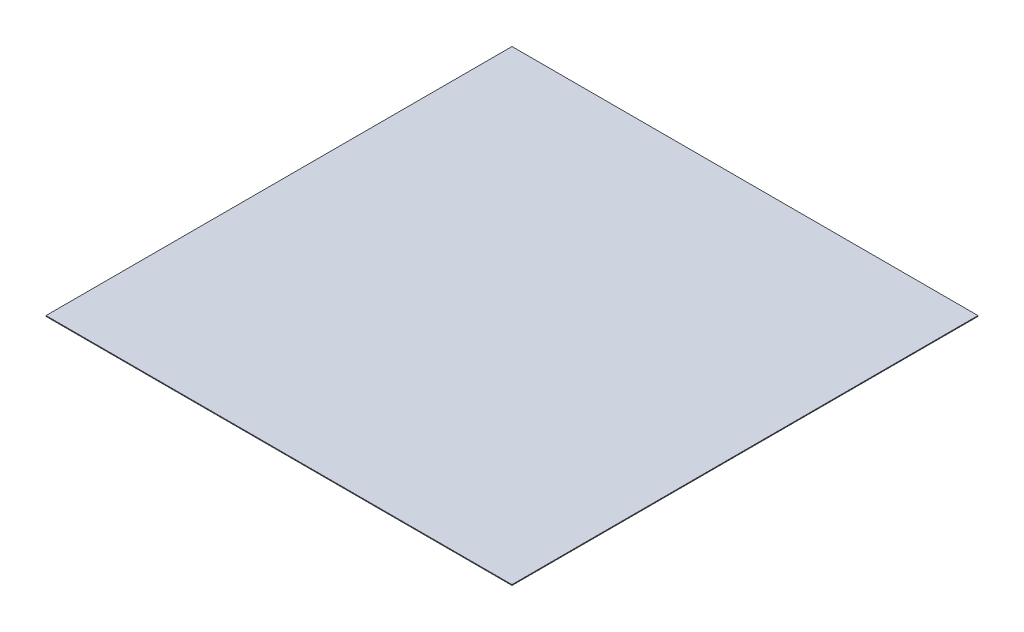
SolidWorks part; units mm, degrees
ref_plane "Front Plane" through (0, 0, 0) normal (0, 0, 1) x (1, 0, 0)
ref_plane "Top Plane" through (0, 0, 0) normal (0, 1, 0) x (1, 0, 0)
ref_plane "Right Plane" through (0, 0, 0) normal (1, 0, 0) x (0, 0, -1)
sketch "Sketch6" plane through (0, 0, 0) normal (0, 1, 0) x (1, 0, 0)
  point P0 (0, 0)
  point P1 (0, 0)
sketch "Sketch3" plane through (0, 0, 0) normal (0, 1, 0) x (1, 0, 0)
  line L1 (-15000, 15000) -> (15000, 15000)
  line L2 (-15000, 15000) -> (-15000, -15000)
  line L3 (-15000, -15000) -> (15000, -15000)
  line L4 (15000, 15000) -> (15000, -15000)
  line L5 (-15000, 15000) -> (15000, -15000) construction
  line L6 (-15000, -15000) -> (15000, 15000) construction
  circle A0 centre (0, 0) radius 254 construction
  point P0 (0, 0)
  point P9 (0, 0)
  dimension "D3" = 508
  dimension "D1" = 30000
  dimension "D2" = 30000
extrude "Boss-Extrude2" add sketch "Sketch3" along normal blind 50
sketch "Sketch8" plane through (0, 0, 0) normal (0, -1, 0) x (1, 0, 0)
  circle A0 centre (0, 215.9) radius 25.4
  circle A1 centre (186.9749, 107.95) radius 25.4
  circle A2 centre (186.9749, -107.95) radius 25.4
  circle A3 centre (0, -215.9) radius 25.4
  circle A4 centre (-186.9749, -107.95) radius 25.4
  circle A5 centre (-186.9749, 107.95) radius 25.4
  point P17 (0, 0)
  dimension "D1" = 50.8
  dimension "D2" = 215.9
  dimension "D3" = 6
extrude "Boss-Extrude4" add sketch "Sketch8" along normal blind 100
sketch "Sketch9" plane through (0, 0, 0) normal (0, -1, 0) x (1, 0, 0)
  line L0 (572.891, 572.891) -> (-761.3105, -761.3105) construction
  line L1 (400, 200) -> (800, 200)
  line L2 (400, 200) -> (400, -200)
  line L3 (400, -200) -> (800, -200)
  line L4 (800, 200) -> (800, -200)
  line L5 (400, 200) -> (800, -200)
  line L6 (400, -200) -> (800, 200) construction
  line L7 (-15000, -15000) -> (15000, 15000) construction
  line L8 (-200, 400) -> (200, 800) construction
  line L9 (200, 400) -> (-200, 800)
  line L10 (200, 800) -> (-200, 800)
  line L11 (-200, 400) -> (-200, 800)
  line L12 (200, 400) -> (200, 800)
  line L13 (200, 400) -> (-200, 400)
  point P0 (600, 0)
  dimension "D1" = 600
  dimension "D2" = 400
  dimension "D3" = 400
extrude "Boss-Extrude5" add sketch "Sketch9" along normal blind 300 contours L5 L2 L3 | L1 L5 L4 | L13 L9 L11 | L9 L12 L10
sketch "Sketch10" plane through (0, -300, 0) normal (0, -1, 0) x (1, 0, 0)
  line L0 (600, 200) -> (600, -200)
  line L1 (400, 200) -> (800, 200) construction
  line L2 (400, -200) -> (800, -200) construction
  line L3 (600, -200) -> (572.891, 0)
  line L4 (572.891, 0) -> (800, 0)
  line L5 (800, 200) -> (800, -200) construction
  line L7 (640, -40) -> (560, -40)
  line L8 (640, -40) -> (640, 40)
  line L9 (640, 40) -> (560, 40)
  line L10 (560, -40) -> (560, 40)
  line L11 (640, -40) -> (560, 40) construction
  line L12 (640, 40) -> (560, -40) construction
  point P6 (600, 0)
  dimension "D1" = 80
  dimension "D2" = 80
extrude "Boss-Extrude6" add sketch "Sketch10" along normal blind 100 separate body contours L10 L9 L8 L7
sketch "Sketch12" plane through (0, -400, 0) normal (0, -1, 0) x (1, 0, 0)
  point P0 (1054.5556, 0)
